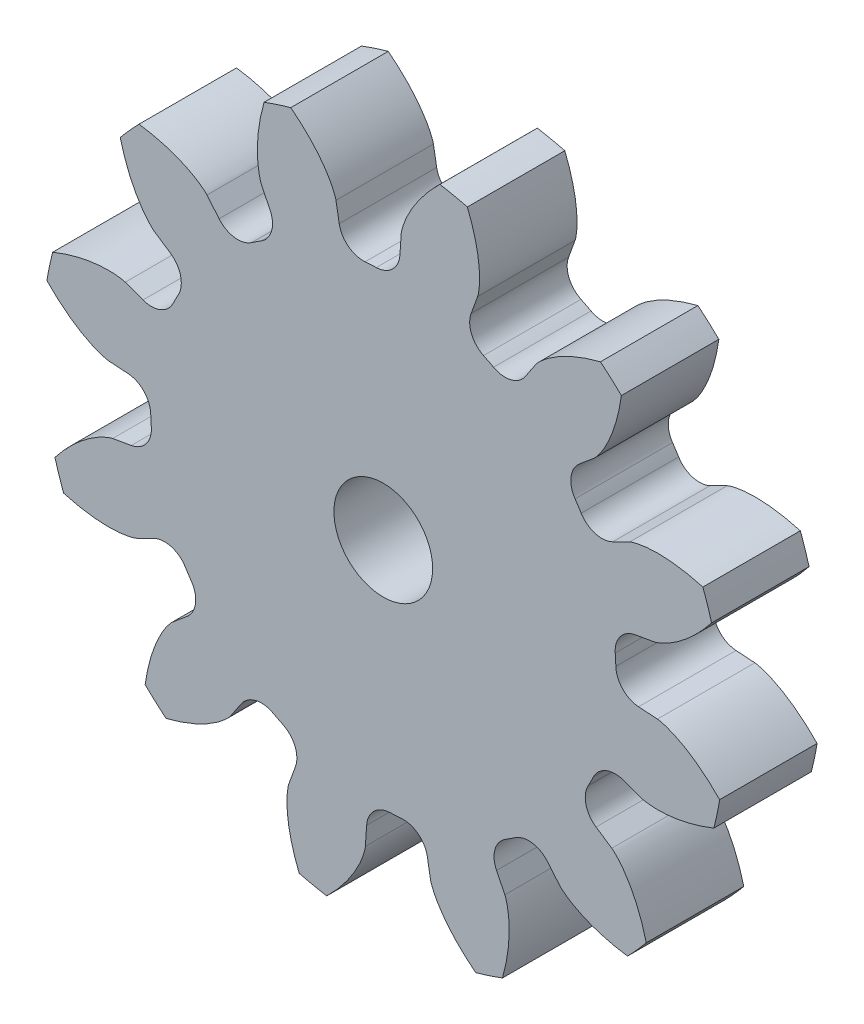
SolidWorks part; units mm, degrees
ref_plane "Plano frontal" through (0, 0, 0) normal (0, 0, 1) x (1, 0, 0)
ref_plane "Plano superior" through (0, 0, 0) normal (0, 1, 0) x (1, 0, 0)
ref_plane "Plano direito" through (0, 0, 0) normal (1, 0, 0) x (0, 0, -1)
sketch "Model" plane through (0, 0, 0) normal (0, 0, 1) x (1, 0, 0)
  line L0 (32.3935, -17.5371) -> (32.1278, -18.2656)
  line L1 (35.2657, -18.9274) -> (35.3168, -18.1536)
  line L2 (37.8078, -18.019) -> (37.9419, -18.7828)
  line L3 (40.9903, -17.787) -> (40.6476, -17.0913)
  line L4 (42.7376, -15.7293) -> (43.2357, -16.3237)
  line L5 (45.3777, -13.9371) -> (44.7331, -13.5059)
  line L6 (45.8621, -11.2815) -> (46.5906, -11.5472)
  line L7 (47.2524, -8.4093) -> (46.4786, -8.3582)
  line L8 (46.344, -5.8672) -> (47.1078, -5.7331)
  line L9 (46.112, -2.6847) -> (45.4163, -3.0274)
  line L10 (44.0543, -0.9374) -> (44.6487, -0.4393)
  line L11 (42.2621, 1.7027) -> (41.8309, 1.0581)
  line L12 (39.6065, 2.1871) -> (39.8722, 2.9156)
  line L13 (36.7343, 3.5774) -> (36.6832, 2.8036)
  line L14 (34.1922, 2.669) -> (34.0581, 3.4328)
  line L15 (31.0097, 2.437) -> (31.3524, 1.7413)
  line L16 (29.2624, 0.3793) -> (28.7643, 0.9737)
  line L17 (26.6223, -1.4129) -> (27.2669, -1.8441)
  line L18 (26.1379, -4.0685) -> (25.4094, -3.8028)
  line L19 (24.7476, -6.9407) -> (25.5214, -6.9918)
  line L20 (25.656, -9.4828) -> (24.8922, -9.6169)
  line L21 (25.888, -12.6653) -> (26.5837, -12.3226)
  line L22 (27.9457, -14.4126) -> (27.3513, -14.9107)
  line L23 (29.7379, -17.0527) -> (30.1691, -16.4081)
  arc A0 (31.4742, -16.0836) -> (31.885, -16.2921) centre (36, -7.675) ccw
  arc A1 (32.3935, -17.5371) -> (31.885, -16.2921) centre (31.4541, -17.1945) ccw
  arc A2 (32.549, -21.243) -> (33.6781, -21.4811) centre (36, -7.675) ccw
  arc A3 (36.2848, -17.22) -> (35.3168, -18.1536) centre (36.3147, -18.2195) ccw
  arc A4 (36.2848, -17.22) -> (36.7448, -17.1951) centre (36, -7.675) ccw
  arc A5 (37.8078, -18.019) -> (36.7448, -17.1951) centre (36.8228, -18.1921) ccw
  arc A6 (39.7953, -21.1507) -> (40.8922, -20.7924) centre (36, -7.675) ccw
  arc A7 (41.0191, -15.7988) -> (40.6476, -17.0913) centre (41.5448, -16.6495) ccw
  arc A8 (41.0191, -15.7988) -> (41.4051, -15.5472) centre (36, -7.675) ccw
  arc A9 (42.7376, -15.7293) -> (41.4051, -15.5472) centre (41.9711, -16.3716) ccw
  arc A10 (46.0247, -17.4477) -> (46.7955, -16.5889) centre (36, -7.675) ccw
  arc A11 (44.4086, -12.2008) -> (44.7331, -13.5059) centre (45.2891, -12.6748) ccw
  arc A12 (44.4086, -12.2008) -> (44.6171, -11.79) centre (36, -7.675) ccw
  arc A13 (45.8621, -11.2815) -> (44.6171, -11.79) centre (45.5195, -12.2209) ccw
  arc A14 (49.568, -11.126) -> (49.8061, -9.9969) centre (36, -7.675) ccw
  arc A15 (45.545, -7.3902) -> (46.4786, -8.3582) centre (46.5445, -7.3603) ccw
  arc A16 (45.545, -7.3902) -> (45.5201, -6.9302) centre (36, -7.675) ccw
  arc A17 (46.344, -5.8672) -> (45.5201, -6.9302) centre (46.5171, -6.8522) ccw
  arc A18 (49.4757, -3.8797) -> (49.1174, -2.7828) centre (36, -7.675) ccw
  arc A19 (44.1238, -2.6559) -> (45.4163, -3.0274) centre (44.9745, -2.1302) ccw
  arc A20 (44.1238, -2.6559) -> (43.8722, -2.2699) centre (36, -7.675) ccw
  arc A21 (44.0543, -0.9374) -> (43.8722, -2.2699) centre (44.6966, -1.7039) ccw
  arc A22 (45.7727, 2.3497) -> (44.9139, 3.1205) centre (36, -7.675) ccw
  arc A23 (40.5258, 0.7336) -> (41.8309, 1.0581) centre (40.9998, 1.6141) ccw
  arc A24 (40.5258, 0.7336) -> (40.115, 0.9421) centre (36, -7.675) ccw
  arc A25 (39.6065, 2.1871) -> (40.115, 0.9421) centre (40.5459, 1.8445) ccw
  arc A26 (39.451, 5.893) -> (38.3219, 6.1311) centre (36, -7.675) ccw
  arc A27 (35.7152, 1.87) -> (36.6832, 2.8036) centre (35.6853, 2.8695) ccw
  arc A28 (35.7152, 1.87) -> (35.2552, 1.8451) centre (36, -7.675) ccw
  arc A29 (34.1922, 2.669) -> (35.2552, 1.8451) centre (35.1772, 2.8421) ccw
  arc A30 (32.2047, 5.8007) -> (31.1078, 5.4424) centre (36, -7.675) ccw
  arc A31 (30.9809, 0.4488) -> (31.3524, 1.7413) centre (30.4552, 1.2995) ccw
  arc A32 (30.9809, 0.4488) -> (30.5949, 0.1972) centre (36, -7.675) ccw
  arc A33 (29.2624, 0.3793) -> (30.5949, 0.1972) centre (30.0289, 1.0216) ccw
  arc A34 (25.9753, 2.0977) -> (25.2045, 1.2389) centre (36, -7.675) ccw
  arc A35 (27.5914, -3.1492) -> (27.2669, -1.8441) centre (26.7109, -2.6752) ccw
  arc A36 (27.5914, -3.1492) -> (27.3829, -3.56) centre (36, -7.675) ccw
  arc A37 (26.1379, -4.0685) -> (27.3829, -3.56) centre (26.4805, -3.1291) ccw
  arc A38 (22.432, -4.224) -> (22.1939, -5.3531) centre (36, -7.675) ccw
  arc A39 (26.455, -7.9598) -> (25.5214, -6.9918) centre (25.4555, -7.9897) ccw
  arc A40 (26.455, -7.9598) -> (26.4799, -8.4198) centre (36, -7.675) ccw
  arc A41 (25.656, -9.4828) -> (26.4799, -8.4198) centre (25.4829, -8.4978) ccw
  arc A42 (22.5243, -11.4703) -> (22.8826, -12.5672) centre (36, -7.675) ccw
  arc A43 (27.8762, -12.6941) -> (26.5837, -12.3226) centre (27.0255, -13.2198) ccw
  arc A44 (27.8762, -12.6941) -> (28.1278, -13.0801) centre (36, -7.675) ccw
  arc A45 (27.9457, -14.4126) -> (28.1278, -13.0801) centre (27.3034, -13.6461) ccw
  arc A46 (26.2273, -17.6997) -> (27.0861, -18.4705) centre (36, -7.675) ccw
  arc A47 (31.4742, -16.0836) -> (30.1691, -16.4081) centre (31.0002, -16.9641) ccw
  circle A48 centre (36, -7.675) radius 2.025
  spline S0 degree 5 number of poles 75 (32.1278, -18.2656) -> (32.549, -21.243)
  spline S1 degree 5 number of poles 75 (33.6781, -21.4811) -> (35.2657, -18.9274)
  spline S2 degree 5 number of poles 75 (37.9419, -18.7828) -> (39.7953, -21.1507)
  spline S3 degree 5 number of poles 75 (40.8922, -20.7924) -> (40.9903, -17.787)
  spline S4 degree 5 number of poles 75 (43.2357, -16.3237) -> (46.0247, -17.4477)
  spline S5 degree 5 number of poles 75 (46.7955, -16.5889) -> (45.3777, -13.9371)
  spline S6 degree 5 number of poles 75 (46.5906, -11.5472) -> (49.568, -11.126)
  spline S7 degree 5 number of poles 75 (49.8061, -9.9969) -> (47.2524, -8.4093)
  spline S8 degree 5 number of poles 75 (47.1078, -5.7331) -> (49.4757, -3.8797)
  spline S9 degree 5 number of poles 75 (49.1174, -2.7828) -> (46.112, -2.6847)
  spline S10 degree 5 number of poles 75 (44.6487, -0.4393) -> (45.7727, 2.3497)
  spline S11 degree 5 number of poles 75 (44.9139, 3.1205) -> (42.2621, 1.7027)
  spline S12 degree 5 number of poles 75 (39.8722, 2.9156) -> (39.451, 5.893)
  spline S13 degree 5 number of poles 75 (38.3219, 6.1311) -> (36.7343, 3.5774)
  spline S14 degree 5 number of poles 75 (34.0581, 3.4328) -> (32.2047, 5.8007)
  spline S15 degree 5 number of poles 75 (31.1078, 5.4424) -> (31.0097, 2.437)
  spline S16 degree 5 number of poles 75 (28.7643, 0.9737) -> (25.9753, 2.0977)
  spline S17 degree 5 number of poles 75 (25.2045, 1.2389) -> (26.6223, -1.4129)
  spline S18 degree 5 number of poles 75 (25.4094, -3.8028) -> (22.432, -4.224)
  spline S19 degree 5 number of poles 75 (22.1939, -5.3531) -> (24.7476, -6.9407)
  spline S20 degree 5 number of poles 75 (24.8922, -9.6169) -> (22.5243, -11.4703)
  spline S21 degree 5 number of poles 75 (22.8826, -12.5672) -> (25.888, -12.6653)
  spline S22 degree 5 number of poles 75 (27.3513, -14.9107) -> (26.2273, -17.6997)
  spline S23 degree 5 number of poles 75 (27.0861, -18.4705) -> (29.7379, -17.0527)
extrude "Ressalto-extrusão1" add sketch "Model" along normal blind 4
